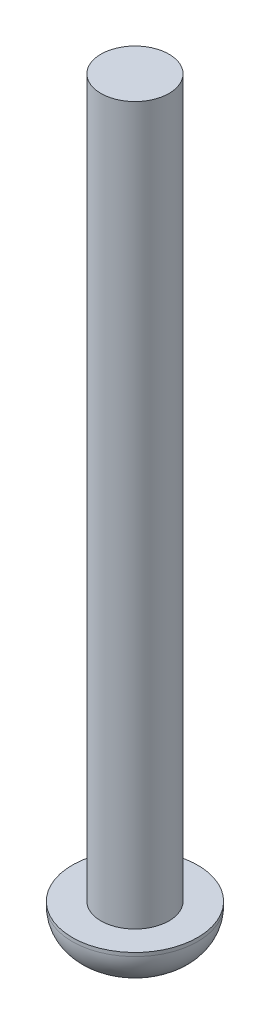
SolidWorks part; units mm, degrees
material "Plain Carbon Steel"
ref_plane "Front Plane" through (0, 0, 0) normal (0, 0, 1) x (1, 0, 0)
ref_plane "Top Plane" through (0, 0, 0) normal (0, 1, 0) x (1, 0, 0)
ref_plane "Right Plane" through (0, 0, 0) normal (1, 0, 0) x (0, 0, -1)
sketch "Sketch1" plane through (0, 0, 0) normal (0, 1, 0) x (1, 0, 0)
  circle A0 centre (0, 0) radius 3.5
  dimension "D1" = 7
extrude "Boss-Extrude1" add sketch "Sketch1" along normal blind 2.2
sketch "Sketch2" plane through (0, 2.2, 0) normal (0, 1, 0) x (1, 0, 0)
  circle A0 centre (0, 0) radius 1.9
  dimension "D1" = 3.8
extrude "Boss-Extrude2" add sketch "Sketch2" along normal blind 40
fillet "Fillet1" radius 2 1 edges at (0, 0, 3.5)
